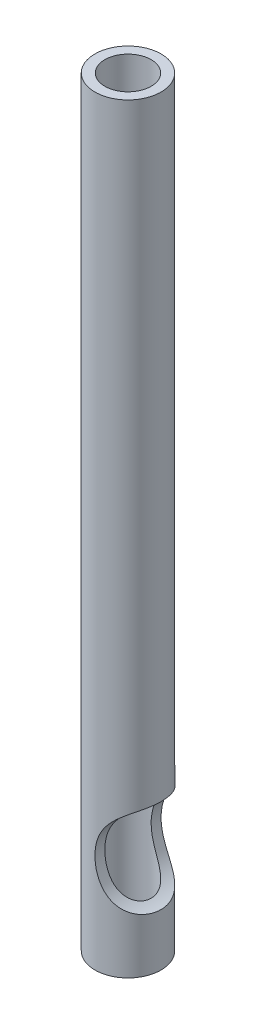
SolidWorks part; units mm, degrees
material "Латунь"
ref_plane "Спереди" through (0, 0, 0) normal (0, 0, 1) x (1, 0, 0)
ref_plane "Сверху" through (0, 0, 0) normal (0, 1, 0) x (1, 0, 0)
ref_plane "Справа" through (0, 0, 0) normal (1, 0, 0) x (0, 0, -1)
sketch "Эскиз1" plane through (0, 0, 0) normal (1, 0, 0) x (0, 0, -1)
  line L0 (0, 0) -> (0, 25) construction
  line L1 (0.7, 13) -> (0, 13)
  line L2 (0.7, 0) -> (0.7, 7)
  line L3 (0.7, 23) -> (1, 23)
  line L4 (1, 23) -> (1, 0)
  line L5 (1, 0) -> (0.7, 0)
  line L6 (0, 13) -> (0, 7)
  line L7 (0, 7) -> (0.7, 7)
  line L8 (0.7, 13) -> (0.7, 23)
  dimension "D1" = 25
  dimension "D2" = 1.4
  dimension "D3" = 2
  dimension "D4" = 23
  dimension "D5" = 10
  dimension "D6" = 7
revolve "Повернуть1" add sketch "Эскиз1" angle 360 about L0
sketch "Эскиз2" plane through (0, 0, 0) normal (0, 0, 1) x (1, 0, 0)
  circle A0 centre (1.5, 3) radius 1.5
  dimension "D2" = 3
  dimension "D1" = 1.5
  dimension "D3" = 3
extrude "Вырез-Вытянуть1" cut sketch "Эскиз2" against normal mid plane 10
